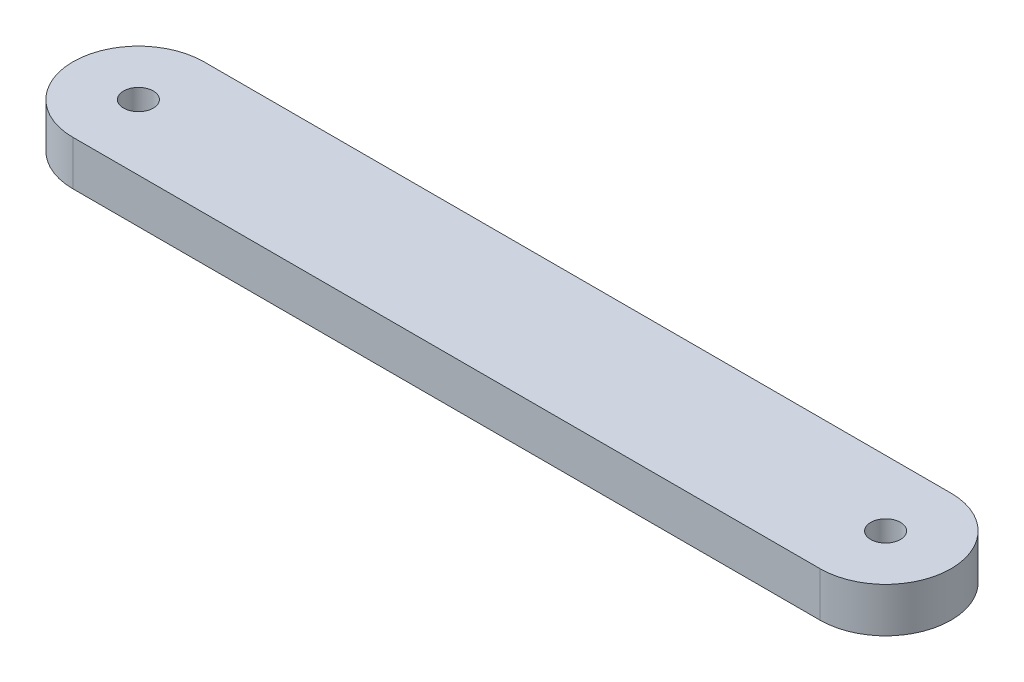
SolidWorks part; units mm, degrees
material "ABS"
ref_plane "前视基准面" through (0, 0, 0) normal (0, 0, 1) x (1, 0, 0)
ref_plane "上视基准面" through (0, 0, 0) normal (0, 1, 0) x (1, 0, 0)
ref_plane "右视基准面" through (0, 0, 0) normal (1, 0, 0) x (0, 0, -1)
other "Configuration Table"
sketch "草图1" plane through (0, 0, 0) normal (0, 1, 0) x (1, 0, 0)
  line L0 (-12.555, 0) -> (12.555, 0) construction
  line L1 (-12.555, 2.2) -> (12.555, 2.2)
  line L2 (-12.555, -2.2) -> (12.555, -2.2)
  arc A0 (-12.555, 2.2) -> (-12.555, -2.2) centre (-12.555, 0) ccw
  arc A1 (12.555, -2.2) -> (12.555, 2.2) centre (12.555, 0) ccw
  circle A2 centre (-12.555, 0) radius 0.5
  circle A3 centre (12.555, 0) radius 0.5
  point P2 (0, 0)
  dimension "D2" = 2.2
  dimension "D3" = 1
  dimension "D4" = 1
  dimension "D1" = 25.11
extrude "凸台-拉伸1" add sketch "草图1" along normal blind 1.5
